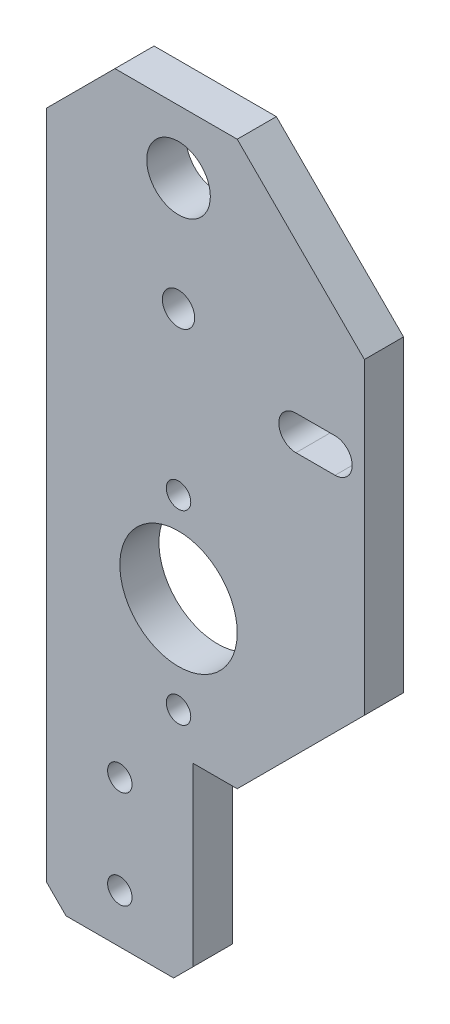
SolidWorks part; units mm, degrees
ref_plane "Front Plane" through (0, 0, 0) normal (0, 0, 1) x (1, 0, 0)
ref_plane "Top Plane" through (0, 0, 0) normal (0, 1, 0) x (1, 0, 0)
ref_plane "Right Plane" through (0, 0, 0) normal (1, 0, 0) x (0, 0, -1)
sketch "Sketch1" plane through (0, 0, 0) normal (0, 0, 1) x (1, 0, 0)
  line L1 (-22.1316, 33.1053) -> (10.3684, 33.1053)
  line L2 (-22.1316, 33.1053) -> (-22.1316, -44.3947)
  line L3 (-7.1316, -24.3947) -> (10.3684, -24.3947)
  line L4 (10.3684, 33.1053) -> (10.3684, -24.3947)
  line L5 (3.3684, 11.8553) -> (7.3684, 11.8553)
  line L7 (-22.1316, -44.3947) -> (-7.1316, -44.3947)
  line L8 (-7.1316, -24.3947) -> (-7.1316, -44.3947)
  line L9 (3.3684, 8.3553) -> (7.3684, 8.3553)
  circle A0 centre (-8.6316, -10.5789) radius 6
  circle A1 centre (-8.6316, 26.6579) radius 3.25
  arc A2 (3.3684, 11.8553) -> (3.3684, 8.3553) centre (3.3684, 10.1053) ccw
  arc A3 (7.3684, 8.3553) -> (7.3684, 11.8553) centre (7.3684, 10.1053) ccw
  dimension "D5" = 12
  dimension "D6" = 6.5
  dimension "D7" = 13.5
  dimension "D1" = 32.5
  dimension "D2" = 77.5
  dimension "D3" = 20
  dimension "D4" = 15
  dimension "D8" = 3.5
  dimension "D9" = 4
  dimension "D10" = 29.5
extrude "Boss-Extrude1" add sketch "Sketch1" along normal blind 4
chamfer "Chamfer1" distance 7 angle 45 1 edges at (-22.1316, 33.1053, 2)
chamfer "Chamfer2" distance 13 angle 45 2 edges at (10.3684, -24.3947, 2) (10.3684, 33.1053, 2)
chamfer "Chamfer3" distance 2 angle 45 2 edges at (-7.1316, -44.3947, 2) (-22.1316, -44.3947, 2)
hole_wizard "M4 Tapped Hole1" positions "Sketch2" profile "Sketch3" tap size "M4" standard "ISO"
sketch "Sketch2" plane through (0, 0, 4) normal (0, 0, 1) x (1, 0, 0)
  line L0 (-22.1316, 26.1053) -> (-22.1316, -42.3947) construction
  line L1 (-20.1316, -44.3947) -> (-9.1316, -44.3947) construction
  point P0 (-8.6316, 15.1053)
  point P9 (-8.6316, 18.0278)
  point P10 (0, 0)
  dimension "D1" = 13.5
  dimension "D2" = 59.5
sketch "Sketch3" plane through (-8.6316, 15.1053, 4) normal (1, 0, 0) x (0, -1, 0)
  line L0 (0, 0) -> (0, 11.0914)
  line L1 (0, 11.0914) -> (1.65, 10.1)
  line L2 (1.65, 10.1) -> (1.65, 0)
  line L5 (1.65, 0) -> (0, 0)
  line L10 (0, 11.0914) -> (-1.65, 10.1) construction
  line L11 (0, -6.35) -> (0, 107.95) construction
  dimension "Tap Drill Dia." = 3.3
  dimension "Tap Drill Depth" = 10.1
  dimension "Drill Angle" = 118
cosmetic thread "Hole Thread1" parameters "D1"=4, "D2"=4
hole_wizard "M3 Tapped Hole1" positions "Sketch4" profile "Sketch5" tap size "M3" standard "ISO"
sketch "Sketch4" plane through (0, 0, 4) normal (0, 0, 1) x (1, 0, 0)
  line L0 (-22.1316, 26.1053) -> (-22.1316, -42.3947) construction
  line L1 (-20.1316, -44.3947) -> (-9.1316, -44.3947) construction
  point P0 (-8.6316, -1.3947)
  point P2 (-8.6316, -20.3947)
  point P4 (-14.6316, -29.3947)
  point P6 (-14.6316, -39.3947)
  point P9 (0, 0)
  point P18 (-16.4027, -39.529)
  dimension "D1" = 13.5
  dimension "D2" = 43
  dimension "D3" = 24
  dimension "D4" = 10
  dimension "D5" = 5
  dimension "D6" = 7.5
  dimension "D7" = 7.5
sketch "Sketch5" plane through (-8.6316, -1.3947, 4) normal (1, 0, 0) x (0, -1, 0)
  line L0 (0, 0) -> (0, 8.2511)
  line L1 (0, 8.2511) -> (1.25, 7.5)
  line L2 (1.25, 7.5) -> (1.25, 0)
  line L5 (1.25, 0) -> (0, 0)
  line L10 (0, 8.2511) -> (-1.25, 7.5) construction
  line L11 (0, -6.35) -> (0, 107.95) construction
  dimension "Tap Drill Dia." = 2.5
  dimension "Tap Drill Depth" = 7.5
  dimension "Drill Angle" = 118
cosmetic thread "Hole Thread2" parameters "D1"=4, "D2"=3
cosmetic thread "Hole Thread3" parameters "D1"=4, "D2"=3
cosmetic thread "Hole Thread4" parameters "D1"=4, "D2"=3
cosmetic thread "Hole Thread5" parameters "D1"=4, "D2"=3
